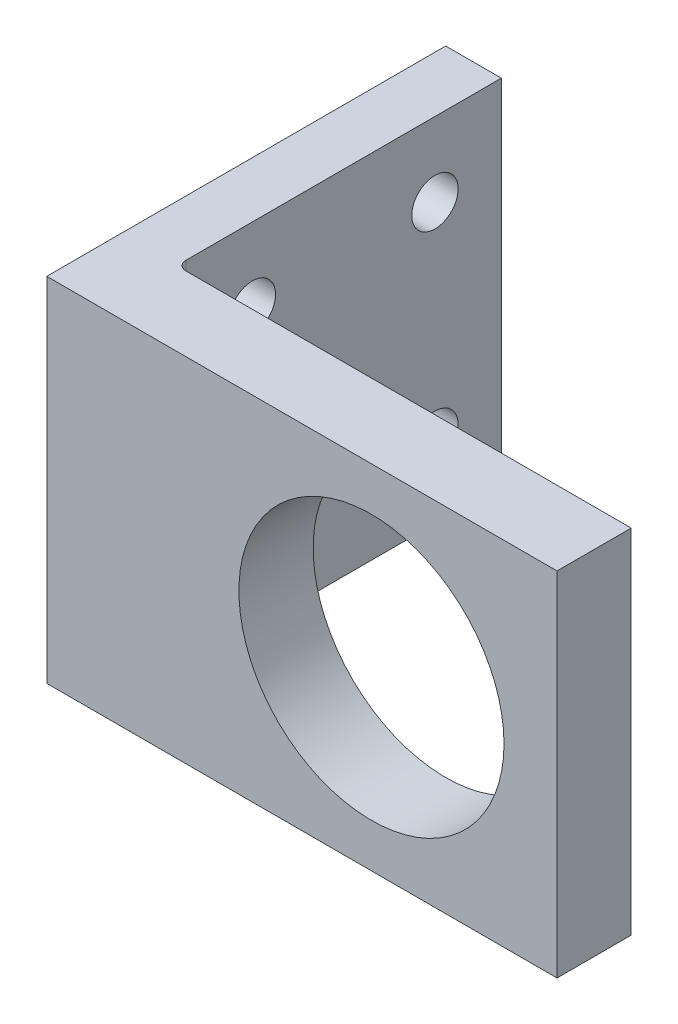
SolidWorks part; units mm, degrees
ref_plane "Piano frontale" through (0, 0, 0) normal (0, 0, 1) x (1, 0, 0)
ref_plane "Piano superiore" through (0, 0, 0) normal (0, 1, 0) x (1, 0, 0)
ref_plane "Piano destro" through (0, 0, 0) normal (1, 0, 0) x (0, 0, -1)
sketch "Sketch1" plane through (0, 0, 0) normal (0, 0, 1) x (1, 0, 0)
  line L0 (0, 19) -> (55, 19) construction
  line L1 (0, 0) -> (55, 0)
  line L2 (0, 0) -> (0, 38)
  line L3 (0, 38) -> (55, 38)
  line L4 (55, 0) -> (55, 38)
  circle A0 centre (35, 19) radius 14.2875
  dimension "D2" = 28.575
  dimension "D1" = 55
  dimension "D3" = 20
  dimension "D8" = 38
extrude "Boss-Extrude3" add sketch "Sketch1" along normal blind 8
sketch "Sketch8" plane through (0, 0, 0) normal (0, 0, -1) x (-1, 0, 0)
  line L0 (-55, 38) -> (0, 38) construction
  line L6 (0, 38) -> (0, 0) construction
  line L7 (-16.35, 19) -> (-35, 19) construction
  line L11 (-18.1947, 25) -> (-18.1947, 24.9954)
  line L12 (0, 0) -> (-55, 0) construction
  line L17 (0, 38) -> (-6, 38)
  line L18 (0, 38) -> (0, 0)
  line L19 (0, 0) -> (-6, 0)
  line L20 (-6, 38) -> (-6, 0)
  dimension "D1" = 6
extrude "Boss-Extrude6" add sketch "Sketch8" along normal blind 35
fillet "Fillet1" radius 1 1 edges at (6, 19, 0)
sketch "Sketch9" plane through (6, 0, 0) normal (1, 0, 0) x (0, 0, -1)
  line L0 (1, 38) -> (35, 0) construction
  line L1 (35, 38) -> (1, 0) construction
  line L2 (35, 38) -> (1, 38) construction
  line L3 (1, 19) -> (35, 19) construction
  line L4 (1, 38) -> (1, 0) construction
  line L5 (35, 38) -> (35, 0) construction
  line L6 (18, 38) -> (18, 0) construction
  line L7 (35, 0) -> (1, 0) construction
  circle A0 centre (8.1579, 30) radius 2.5
  circle A1 centre (8.1579, 8) radius 2.5
  circle A2 centre (27.8421, 8) radius 2.5
  circle A3 centre (27.8421, 30) radius 2.5
  dimension "D1" = 5
  dimension "D2" = 8
extrude "Cut-Extrude1" cut sketch "Sketch9" against normal blind 10
